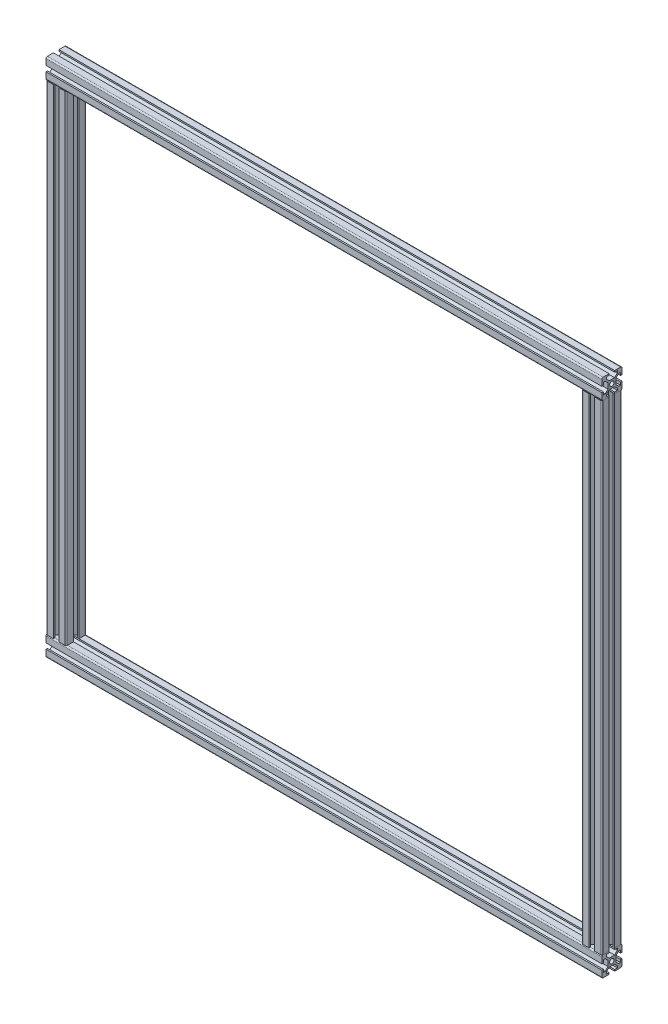
SolidWorks part; units mm, degrees
material "6061-T6 (SS)"
ref_plane "Front Plane" through (0, 0, 0) normal (0, 0, 1) x (1, 0, 0)
ref_plane "Top Plane" through (0, 0, 0) normal (0, 1, 0) x (1, 0, 0)
ref_plane "Right Plane" through (0, 0, 0) normal (1, 0, 0) x (0, 0, -1)
sketch3d "3DSketch1"
  line L0 (0, 0, 0) -> (798, 0, 0)
  line L1 (798, 0, 0) -> (798, 745, 0)
  line L2 (798, 745, 0) -> (0, 745, 0)
  line L3 (0, 745, 0) -> (0, 0, 0)
  dimension "D1" = 798
  dimension "D2" = 745
other "4040 3030_EX(1)"
ref_plane "Plane3" through (798, 745, 0) normal (-1, 0, 0) x (0, 0, 1)
sketch "Sketch21" plane through (798, 745, 0) normal (-1, 0, 0) x (0, 0, 1)
  line L0 (0, 15) -> (0, -15) construction
  line L1 (15, 0) -> (-15, 0) construction
  line L2 (4.0239, 5.82) -> (-4.0239, 5.82)
  line L3 (-4.0239, 5.82) -> (-8.255, 10.0511)
  line L4 (-8.255, 10.0511) -> (-8.255, 12.79)
  line L5 (-8.255, 12.79) -> (-4.065, 12.79)
  line L6 (-4.065, 12.79) -> (-4.065, 15)
  line L7 (-4.065, 15) -> (-13, 15)
  line L8 (-15, 13) -> (-15, 4.065)
  line L9 (-15, 4.065) -> (-12.79, 4.065)
  line L10 (-12.79, 4.065) -> (-12.79, 8.255)
  line L11 (-12.79, 8.255) -> (-10.0511, 8.255)
  line L12 (-10.0511, 8.255) -> (-5.82, 4.0239)
  line L13 (-5.82, 4.0239) -> (-5.82, -4.0239)
  line L14 (0, 0) -> (-13, 13) construction
  line L15 (5.82, 4.0239) -> (5.82, -4.0239)
  line L16 (4.0239, 5.82) -> (8.255, 10.0511)
  line L17 (10.0511, 8.255) -> (5.82, 4.0239)
  line L18 (15, 4.065) -> (12.79, 4.065)
  line L19 (12.79, 4.065) -> (12.79, 8.255)
  line L20 (12.79, 8.255) -> (10.0511, 8.255)
  line L21 (8.255, 10.0511) -> (8.255, 12.79)
  line L22 (4.065, 12.79) -> (4.065, 15)
  line L23 (8.255, 12.79) -> (4.065, 12.79)
  line L24 (4.065, 15) -> (13, 15)
  line L25 (15, 13) -> (15, 4.065)
  line L26 (0, 0) -> (13, 13) construction
  line L27 (-5.82, 4.0239) -> (-4.0239, 5.82) construction
  line L28 (15, -4.065) -> (12.79, -4.065)
  line L29 (12.79, -8.255) -> (10.0511, -8.255)
  line L30 (12.79, -4.065) -> (12.79, -8.255)
  line L31 (15, -13) -> (15, -4.065)
  line L32 (4.065, -15) -> (13, -15)
  line L33 (4.065, -12.79) -> (4.065, -15)
  line L34 (8.255, -12.79) -> (4.065, -12.79)
  line L35 (8.255, -10.0511) -> (8.255, -12.79)
  line L36 (4.0239, -5.82) -> (8.255, -10.0511)
  line L37 (10.0511, -8.255) -> (5.82, -4.0239)
  line L38 (-4.0239, -5.82) -> (-8.255, -10.0511)
  line L39 (4.0239, -5.82) -> (-4.0239, -5.82)
  line L40 (-10.0511, -8.255) -> (-5.82, -4.0239)
  line L41 (-15, -4.065) -> (-12.79, -4.065)
  line L42 (-12.79, -4.065) -> (-12.79, -8.255)
  line L43 (-12.79, -8.255) -> (-10.0511, -8.255)
  line L44 (-4.065, -12.79) -> (-4.065, -15)
  line L45 (-8.255, -10.0511) -> (-8.255, -12.79)
  line L46 (-8.255, -12.79) -> (-4.065, -12.79)
  line L47 (-4.065, -15) -> (-13, -15)
  line L48 (-15, -13) -> (-15, -4.065)
  circle A1 centre (0, 0) radius 3.325
  arc A2 (-13, 15) -> (-15, 13) centre (-13, 13) ccw
  arc A4 (13, 15) -> (15, 13) centre (13, 13) cw
  arc A7 (13, -15) -> (15, -13) centre (13, -13) ccw
  arc A8 (-13, -15) -> (-15, -13) centre (-13, -13) cw
  point P2 (0, 0)
  point P5 (0, 0)
  point P9 (0, 0)
  point P27 (0, 5.82)
  point P54 (5.82, 0)
  point P55 (-5.82, 0)
  point P68 (-15, -15)
  point P69 (0, 0)
  point P70 (15, 0)
  point P71 (0, -15)
  point P72 (-15, 0)
  point P73 (0, 15)
  point P74 (0, 0)
  point P75 (-15, 15)
  point P76 (15, 15)
  point P77 (15, -15)
  dimension "D1" = 6.65
  dimension "D7" = 2
  dimension "D2" = 30
  dimension "D3" = 45
  dimension "D4" = 9.18
  dimension "D5" = 4.065
  dimension "D6" = 2.21
  dimension "D9" = 16.51
  dimension "D10" = 2.54
equation "\"W\"= 1700"
equation "\"L\"= 760"
equation "\"H\"= 810"
equation "\"ARM_BOLT_SPACING\"= 166"
equation "\"ARM_TO_WALL\"= 300"
equation "\"D1@3DSketch1\"=(\"W\"/2)-52"
equation "\"D2@3DSketch1\"=\"H\"-65"
